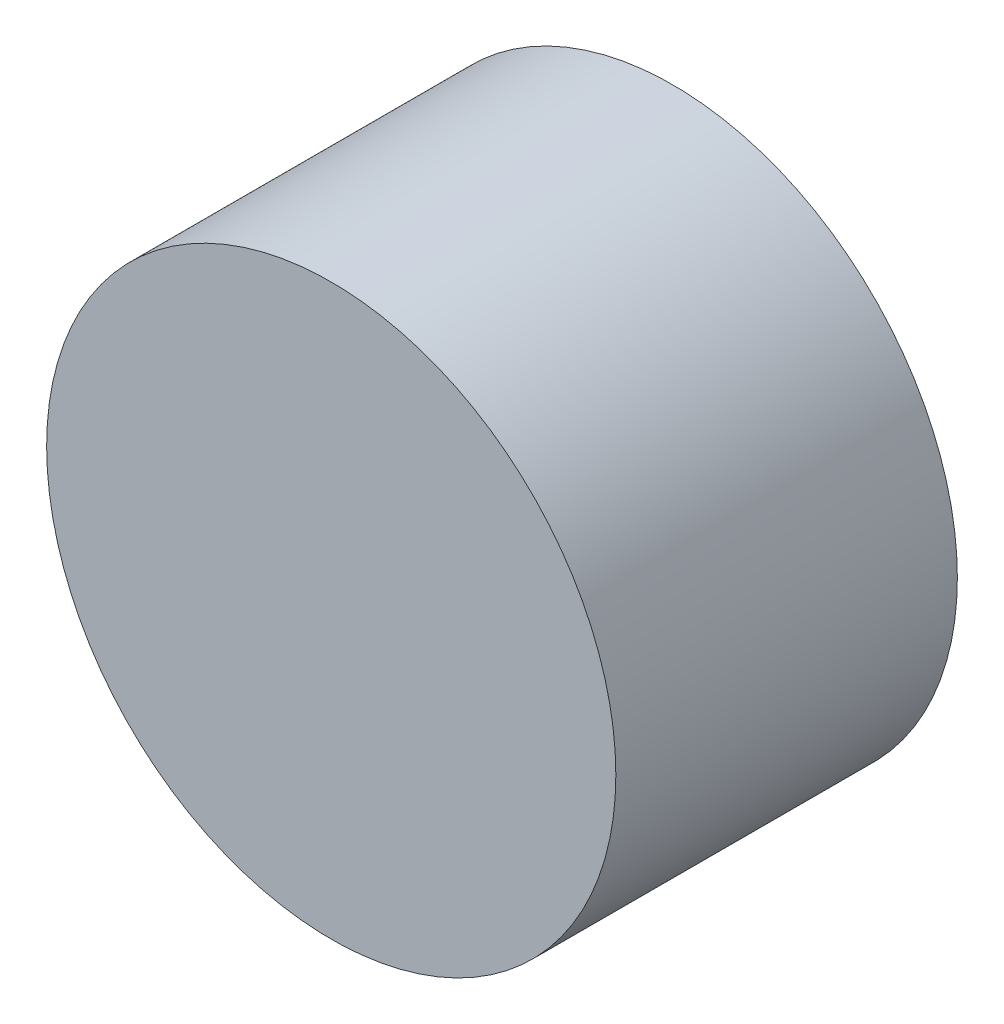
SolidWorks part; units mm, degrees
ref_plane "Front Plane" through (0, 0, 0) normal (0, 0, 1) x (1, 0, 0)
ref_plane "Top Plane" through (0, 0, 0) normal (0, 1, 0) x (1, 0, 0)
ref_plane "Right Plane" through (0, 0, 0) normal (1, 0, 0) x (0, 0, -1)
sketch "Sketch1" plane through (0, 0, 0) normal (0, 0, 1) x (1, 0, 0)
  circle A0 centre (0, 0) radius 2.5
  dimension "D1" = 5
extrude "Boss-Extrude1" add sketch "Sketch1" along normal mid plane 3
ref_plane "Plane1" through (0, 0, 2.5) normal (0, 0, 1) x (1, 0, 0)
sketch "Sketch2" plane through (0, 0, 2.5) normal (0, 0, 1) x (1, 0, 0)
  line L0 (2.5, 0) -> (2.5, -0.125)
  line L1 (2.5, 0) -> (2.5, 0.125)
  circle A0 centre (0, 0) radius 2.5 construction
  point P0 (2.5, 0)
  dimension "D1" = 0.25
